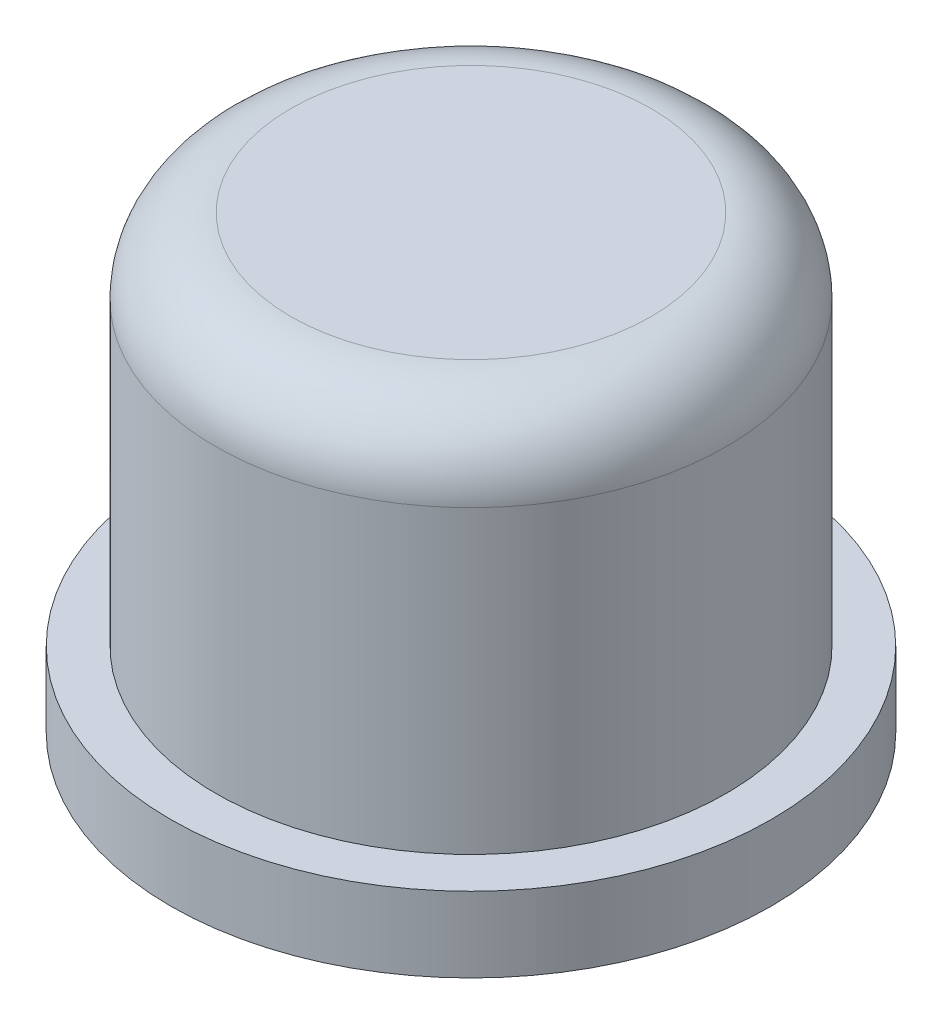
SolidWorks part; units mm, degrees
ref_plane "Front Plane" through (0, 0, 0) normal (0, 0, 1) x (1, 0, 0)
ref_plane "Top Plane" through (0, 0, 0) normal (0, 1, 0) x (1, 0, 0)
ref_plane "Right Plane" through (0, 0, 0) normal (1, 0, 0) x (0, 0, -1)
sketch "Sketch1" plane through (0, 0, 0) normal (0, 0, 1) x (1, 0, 0)
  line L0 (0, 3) -> (0, 12.8532) construction
  line L1 (0, 6) -> (-3.4, 6)
  line L2 (-3.4, 6) -> (-3.4, 1)
  line L3 (-3.4, 1) -> (-4, 1)
  line L4 (-4, 1) -> (-4, 0)
  line L5 (-4, 0) -> (-2.25, 0)
  line L6 (0, 3) -> (0, 6)
  line L7 (-2.25, 0) -> (-2.25, 3)
  line L8 (-2.25, 3) -> (0, 3)
  line L9 (-2.25, 0) -> (0, 0) construction
  line L10 (0, 0) -> (0, 3) construction
  dimension "D1" = 6.8
  dimension "D2" = 1
  dimension "D3" = 8
  dimension "D4" = 5
  dimension "D5" = 3
  dimension "D6" = 4.5
revolve "Revolve1" add sketch "Sketch1" angle 360 about L0
fillet "Fillet1" radius 1 1 edges at (0, 6, -3.4)
